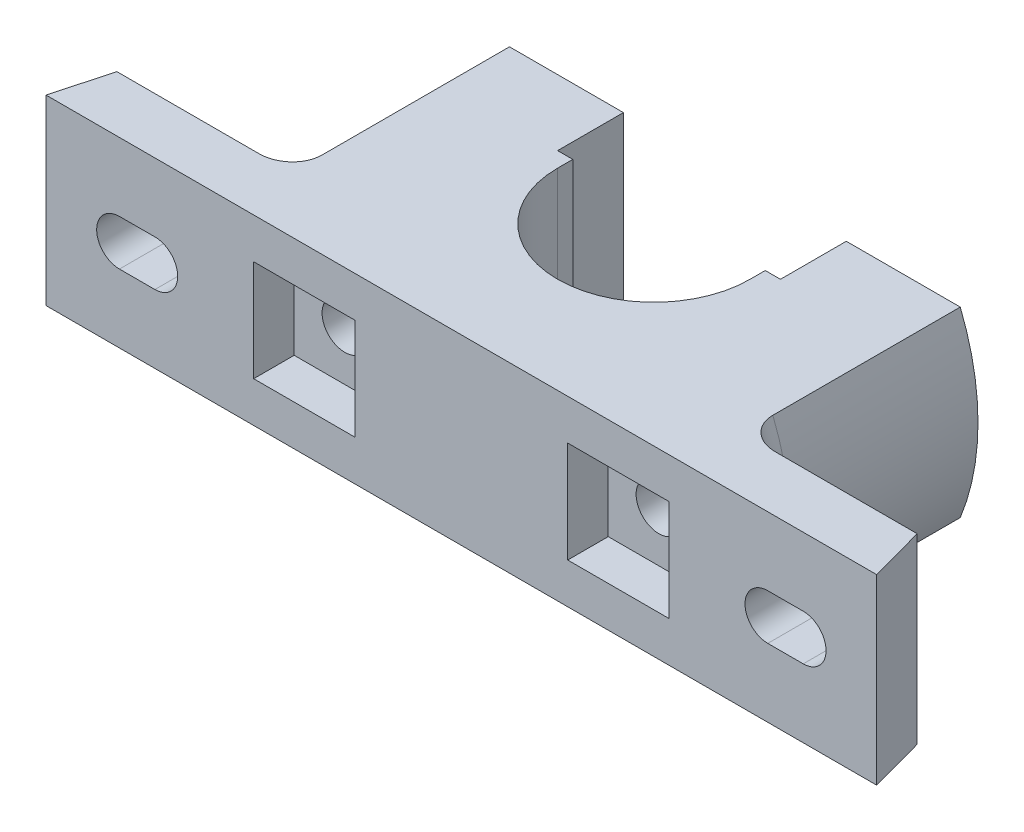
SolidWorks part; units mm, degrees
ref_plane "Front Plane" through (0, 0, 0) normal (0, 0, 1) x (1, 0, 0)
ref_plane "Top Plane" through (0, 0, 0) normal (0, 1, 0) x (1, 0, 0)
ref_plane "Right Plane" through (0, 0, 0) normal (1, 0, 0) x (0, 0, -1)
sketch "Sketch1" plane through (0, 0, 0) normal (0, 1, 0) x (1, 0, 0)
  line L0 (0, 38) -> (0, -42.7499) construction
  line L1 (-82, 0) -> (82, 0)
  line L2 (50, 11) -> (79, 11)
  line L3 (79, 11) -> (82, 0)
  line L4 (50, 11) -> (50, 54)
  line L5 (50, 54) -> (22, 54)
  line L6 (22, 54) -> (22, 41)
  line L7 (22, 41) -> (19, 41)
  line L8 (-22, 41) -> (-19, 41)
  line L9 (-22, 54) -> (-22, 41)
  line L10 (-50, 54) -> (-22, 54)
  line L11 (-50, 11) -> (-50, 54)
  line L12 (-50, 11) -> (-79, 11)
  line L13 (-79, 11) -> (-82, 0)
  line L14 (19, 38) -> (19, 41)
  line L15 (-19, 38) -> (-19, 41)
  arc A0 (-19, 38) -> (19, 38) centre (0, 38) ccw
  point P18 (0, 0)
  dimension "D4" = 54
  dimension "D7" = 16
  dimension "D9" = 19
  dimension "D2" = 3
  dimension "D3" = 13
  dimension "D5" = 50
  dimension "D6" = 44
  dimension "D8" = 11
  dimension "D10" = 38
  dimension "D11" = 164
extrude "Boss-Extrude1" add sketch "Sketch1" along normal mid plane 36
sketch "Sketch3" plane through (0, 0, 0) normal (0, 0, 1) x (1, 0, 0)
  line L2 (-41, 10) -> (-21, 10)
  line L3 (-41, 10) -> (-41, -10)
  line L4 (-41, -10) -> (-21, -10)
  line L5 (-21, 10) -> (-21, -10)
  line L6 (-41, 10) -> (-21, -10) construction
  line L7 (-41, -10) -> (-21, 10) construction
  point P0 (-31, 0)
  dimension "D1" = 31
  dimension "D2" = 20
extrude "Cut-Extrude3" cut sketch "Sketch3" against normal blind 8
sketch "Sketch5" plane through (0, 0, -8) normal (0, 0, 1) x (1, 0, 0)
  circle A0 centre (-31, 0) radius 4.5
  dimension "D1" = 9
  dimension "D2" = 31
extrude "Cut-Extrude4" cut sketch "Sketch5" against normal through all
sketch "Sketch2" plane through (0, 0, -54) normal (0, 0, -1) x (-1, 0, 0)
  line L0 (50, 18) -> (50, -18) construction
  line L1 (-50, 18) -> (-50, -18) construction
  line L2 (50, 18) -> (50, -18)
  line L3 (-50, 18) -> (-50, -18)
  line L4 (-50, -18) -> (-22, -18) construction
  line L5 (-50, 18) -> (-22, 18) construction
  line L6 (22, 18) -> (50, 18) construction
  line L7 (22, -18) -> (50, -18) construction
  line L8 (-50, -18) -> (-44.4972, -18)
  line L9 (-50, 18) -> (-44.4972, 18)
  line L10 (44.4972, 18) -> (50, 18)
  line L11 (44.4972, -18) -> (50, -18)
  arc A0 (44.4972, -18) -> (44.4972, 18) centre (0, 0) ccw
  arc A1 (-44.4972, 18) -> (-44.4972, -18) centre (0, 0) ccw
  line M1 (22, -18) -> (50, -18)
  line M2 (50, -18) -> (50, 18)
  line M3 (50, 18) -> (22, 18)
  dimension "D1" = 96
extrude "Cut-Extrude1" cut sketch "Sketch2" against normal up to surface (43 mm away) contours A0 M1 M2 M3 | A1 L9 L3 L8 up to face at (-64.5, 0, -11)
fillet "Fillet1" radius 6 2 edges at (-48, 0, -11) (48, 0, -11)
sketch "Sketch6" plane through (0, 0, 0) normal (0, 0, 1) x (1, 0, 0)
  line L0 (-60.5, 0) -> (-67.5, 0) construction
  line L1 (-60.5, -4.5) -> (-67.5, -4.5)
  line L2 (-60.5, 4.5) -> (-67.5, 4.5)
  arc A0 (-60.5, -4.5) -> (-60.5, 4.5) centre (-60.5, 0) ccw
  arc A1 (-67.5, 4.5) -> (-67.5, -4.5) centre (-67.5, 0) ccw
  point P3 (-64, 0)
  dimension "D1" = 9
  dimension "D2" = 16
  dimension "D3" = 64
extrude "Cut-Extrude5" cut sketch "Sketch6" against normal through all
sketch "Sketch8" plane through (0, 0, 0) normal (0, 0, 1) x (1, 0, 0)
  circle A0 centre (31, 0) radius 4.5
  dimension "D1" = 9
  dimension "D2" = 31
extrude "Cut-Extrude6" cut sketch "Sketch8" against normal through all
sketch "Sketch9" plane through (0, 0, 0) normal (0, 0, 1) x (1, 0, 0)
  line L0 (-82, -18) -> (82, -18) construction
  line L1 (21, 10) -> (41, 10)
  line L2 (21, 10) -> (21, -10)
  line L3 (21, -10) -> (41, -10)
  line L4 (41, 10) -> (41, -10)
  dimension "D1" = 20
  dimension "D2" = 8
  dimension "D3" = 21
extrude "Cut-Extrude7" cut sketch "Sketch9" against normal blind 8
hole_wizard "Ø6.0mm Dowel Hole1" positions "3DSketch3" profile "Sketch13" hole size "Ø6.0" standard "ANSI Metric"
sketch3d "3DSketch3"
  point P0 (0, 0, -19)
  dimension "D1" = 0
  dimension "D2" = 0
sketch "Sketch13" plane through (0, 0, -19) normal (1, 0, 0) x (0, 1, 0)
  line L0 (0, 0) -> (0, 7.8026)
  line L1 (0, 7.8026) -> (3, 6)
  line L2 (3, 6) -> (3, 0)
  line L5 (3, 0) -> (0, 0)
  line L10 (0, 7.8026) -> (-3, 6) construction
  line L11 (0, -6.35) -> (0, 107.95) construction
  dimension "Hole Dia." = 6
  dimension "Hole Depth" = 6
  dimension "Drill Angle" = 118
mirror "Mirror3" about plane through (0, 0, 0) normal (1, 0, 0) of "Cut-Extrude5"
